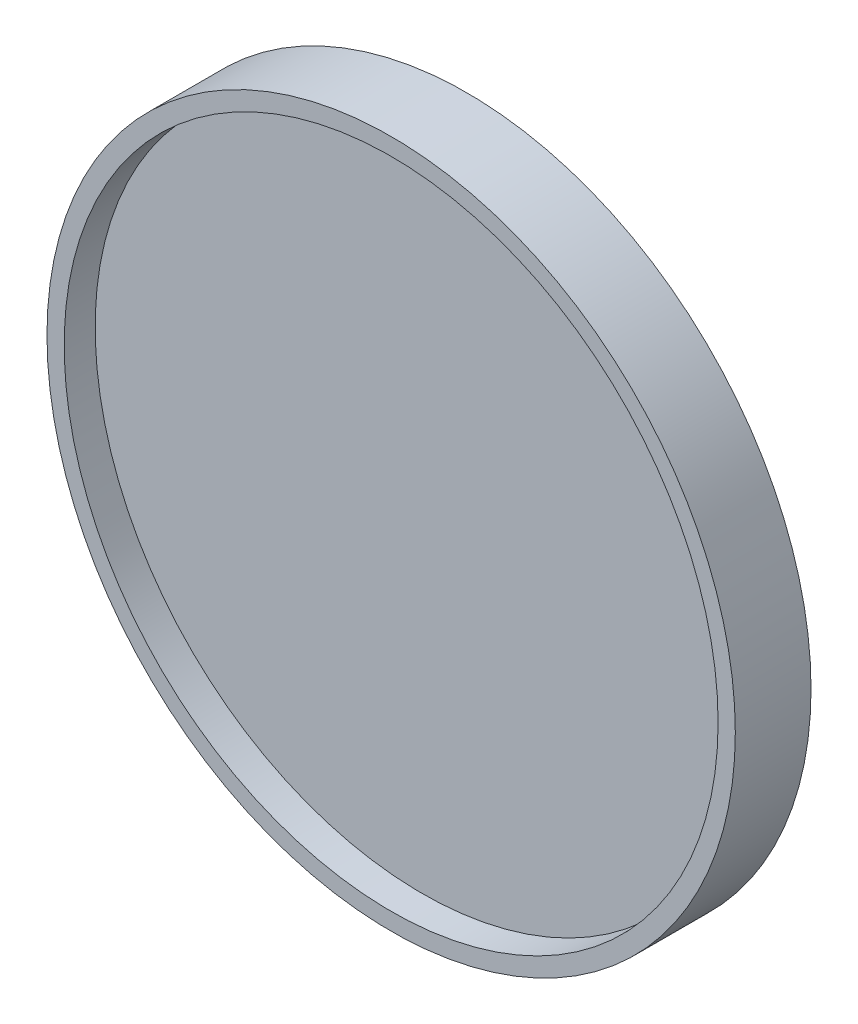
SolidWorks part; units mm, degrees
ref_plane "Front Plane" through (0, 0, 0) normal (0, 0, 1) x (1, 0, 0)
ref_plane "Top Plane" through (0, 0, 0) normal (0, 1, 0) x (1, 0, 0)
ref_plane "Right Plane" through (0, 0, 0) normal (1, 0, 0) x (0, 0, -1)
sketch "Sketch1" plane through (0, 0, 0) normal (0, 0, 1) x (1, 0, 0)
  circle A0 centre (0, 0) radius 25
  circle A1 centre (0, 0) radius 23.75
  dimension "D1" = 47.5
  dimension "D2" = 50
extrude "Boss-Extrude1" add sketch "Sketch1" along normal mid plane 5.5
sketch "Sketch2" plane through (0, 0, 0) normal (0, 0, 1) x (1, 0, 0)
  circle A0 centre (0, 0) radius 23.75
extrude "Boss-Extrude2" add sketch "Sketch2" along normal mid plane 1
